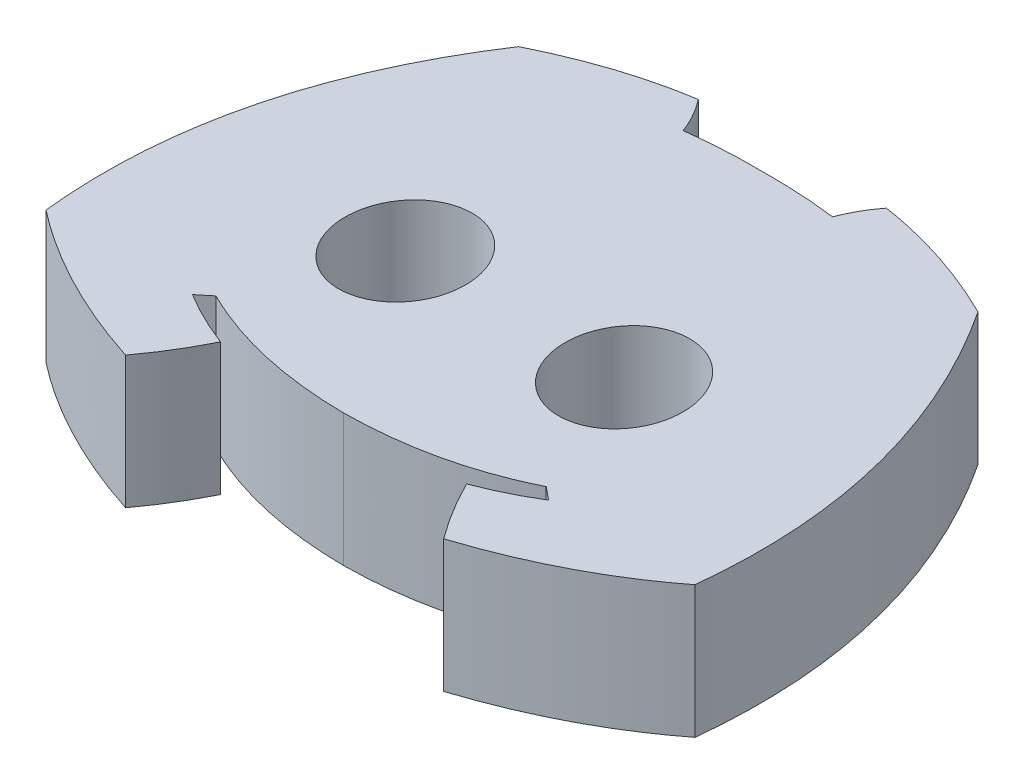
SolidWorks part; units mm, degrees
ref_plane "Front Plane" through (0, 0, 0) normal (0, 0, 1) x (1, 0, 0)
ref_plane "Top Plane" through (0, 0, 0) normal (0, 1, 0) x (1, 0, 0)
ref_plane "Right Plane" through (0, 0, 0) normal (1, 0, 0) x (0, 0, -1)
sketch "Sketch1" plane through (0, 0, 0) normal (0, 1, 0) x (1, 0, 0)
  line L0 (341.3492, 576.008) -> (1706.6826, 576.008) construction
  line L1 (0.9093, 0.9722) -> (15.1324, 8.9689) construction
  line L2 (15.1314, 0.9722) -> (0.9093, 8.9722) construction
  line L3 (8.0208, 4.9706) -> (8.0208, 8.9722) construction
  line L4 (8.0208, 4.9706) -> (8.1028, 1.051) construction
  ellipse E0 centre (6.3665, 4.6104) end of major axis (6.4122, 5.6112) minor radius 0.9004
  ellipse E1 centre (9.6752, 4.6104) end of major axis (9.6295, 5.6112) minor radius 0.9004
  spline S0 degree 2 poles (8.0825, 2.0216) (6.6629, 2.0216) (5.5233, 2.5897) knots 0 0 0 1 1 1
  spline S1 degree 1 poles (5.5233, 2.5897) (5.3274, 2.4298) knots 0 0 1 1
  spline S2 degree 2 poles (5.3274, 2.4298) (5.711, 2.193) (6.16, 2.0216) knots 0 0 0 1 1 1
  spline S3 degree 2 poles (6.16, 2.0216) (5.9192, 1.54) (5.6147, 1.1303) knots 0 0 0 1 1 1
  spline S4 degree 2 poles (5.6147, 1.1303) (4.1821, 1.5958) (3.1121, 2.4298) knots 0 0 0 1 1 1
  spline S5 degree 2 poles (3.1121, 2.4298) (2.7905, 5.4769) (4.5464, 8.1441) knots 0 0 0 1 1 1
  spline S6 degree 2 poles (4.5464, 8.1441) (5.5819, 8.657) (6.5985, 8.8095) knots 0 0 0 1 1 1
  spline S7 degree 2 poles (6.5985, 8.8095) (6.7838, 8.5756) (6.8902, 8.2888) knots 0 0 0 1 1 1
  spline S8 degree 2 poles (6.8902, 8.2888) (7.4547, 8.3601) (8.0208, 8.3513) knots 0 0 0 1 1 1
  spline S9 degree 2 poles (9.1515, 8.2888) (8.587, 8.3601) (8.0208, 8.3513) knots 0 0 0 1 1 1
  spline S10 degree 2 poles (9.4431, 8.8095) (9.2579, 8.5756) (9.1515, 8.2888) knots 0 0 0 1 1 1
  spline S11 degree 2 poles (11.4953, 8.1441) (10.4598, 8.657) (9.4431, 8.8095) knots 0 0 0 1 1 1
  spline S12 degree 2 poles (12.9296, 2.4298) (13.2512, 5.4769) (11.4953, 8.1441) knots 0 0 0 1 1 1
  spline S13 degree 2 poles (10.427, 1.1303) (11.8596, 1.5958) (12.9296, 2.4298) knots 0 0 0 1 1 1
  spline S14 degree 2 poles (9.8817, 2.0216) (10.1225, 1.54) (10.427, 1.1303) knots 0 0 0 1 1 1
  spline S15 degree 2 poles (10.7143, 2.4298) (10.3307, 2.193) (9.8817, 2.0216) knots 0 0 0 1 1 1
  spline S16 degree 1 poles (10.5184, 2.5897) (10.7143, 2.4298) knots 0 0 1 1
  spline S17 degree 2 poles (7.9591, 2.0216) (9.3788, 2.0216) (10.5184, 2.5897) knots 0 0 0 1 1 1
extrude "Boss-Extrude1" add sketch "Sketch1" along normal blind 2 contours S0 S17 S16 S15 S14 S13 S12 S11 S10 S9 S8 S7 S6 S5 S4 S3 S2 S1 E1 E0
